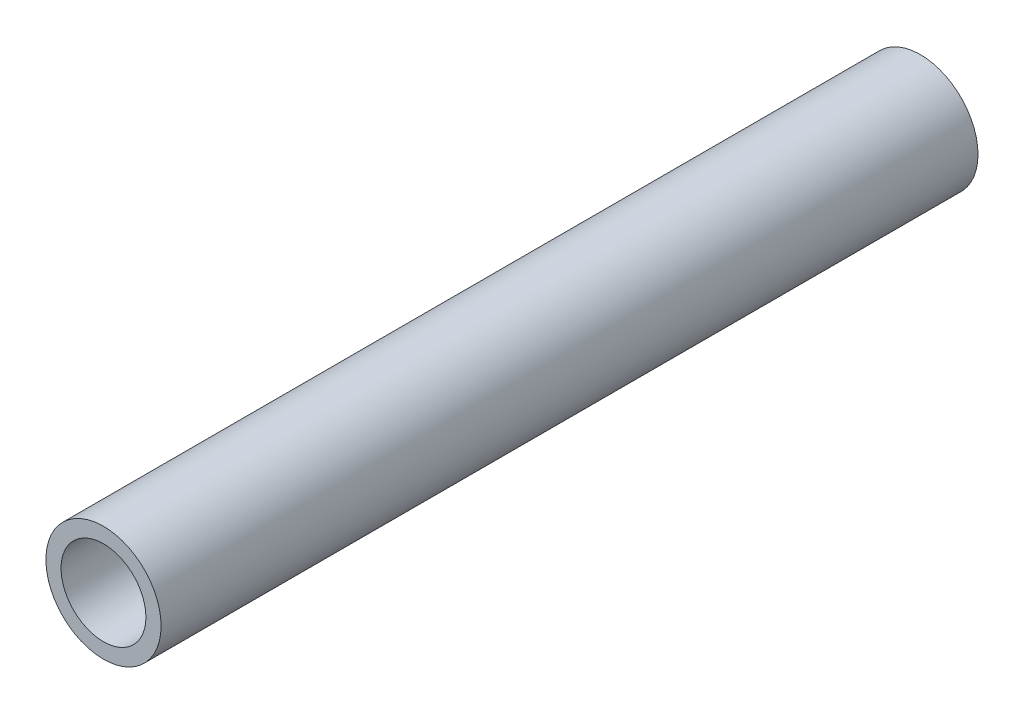
SolidWorks part; units mm, degrees
ref_plane "Front Plane" through (0, 0, 0) normal (0, 0, 1) x (1, 0, 0)
ref_plane "Top Plane" through (0, 0, 0) normal (0, 1, 0) x (1, 0, 0)
ref_plane "Right Plane" through (0, 0, 0) normal (1, 0, 0) x (0, 0, -1)
sketch "Sketch1" plane through (0, 0, 0) normal (0, 0, 1) x (1, 0, 0)
  circle A0 centre (0, 0) radius 4.826
  circle A1 centre (0, 0) radius 3.556
  dimension "D1" = 7.112
  dimension "D2" = 1.27
extrude "Boss-Extrude1" add sketch "Sketch1" along normal blind 68.453
